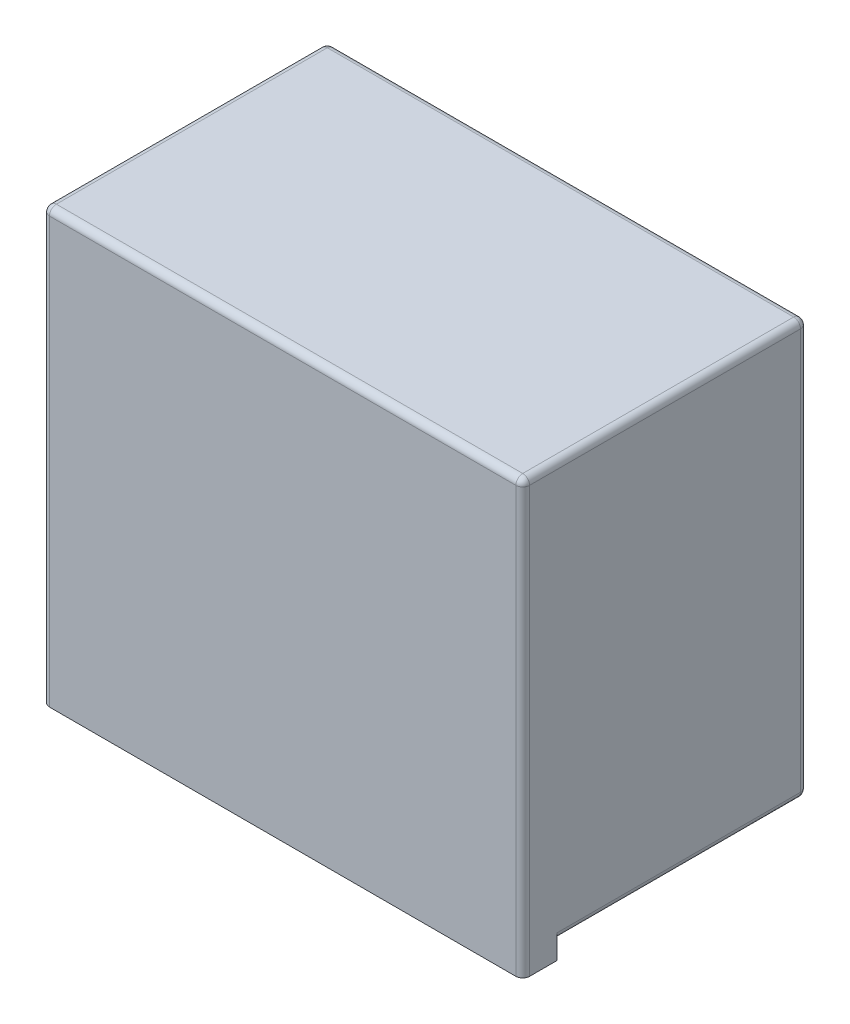
SolidWorks part; units mm, degrees
material "Duranickel(R) 301"
ref_plane "Alzado" through (0, 0, 0) normal (0, 0, 1) x (1, 0, 0)
ref_plane "Planta" through (0, 0, 0) normal (0, 1, 0) x (1, 0, 0)
ref_plane "Vista lateral" through (0, 0, 0) normal (1, 0, 0) x (0, 0, -1)
sketch "Croquis1" plane through (0, 0, 0) normal (0, 0, 1) x (1, 0, 0)
  line L1 (0, 0) -> (14, 0)
  line L2 (0, 0) -> (0, 12.6)
  line L3 (0, 12.6) -> (14, 12.6)
  line L4 (14, 0) -> (14, 12.6)
  dimension "D1" = 14
  dimension "D2" = 12.6
extrude "Extruir1" add sketch "Croquis1" along normal blind 8.3
sketch "Croquis2" plane through (0, 0, 0) normal (0, 0, -1) x (-1, 0, 0)
  line L0 (-14.677, 10.9) -> (-1.1655, 10.9) construction
  line L1 (-14, 12.6) -> (0, 12.6) construction
  line L2 (-7, 0) -> (-7, -0.6221) construction
  line L3 (0, 0) -> (-14, 0) construction
  circle A0 centre (-7, 6.15) radius 4.75
  dimension "D1" = 9.5
  dimension "D2" = 1.7
extrude "Cortar-Extruir1" cut sketch "Croquis2" against normal blind 7.3
fillet "Redondeo1" radius 0.5 1 edges at (2.25, 6.15, 0)
sketch "Croquis3" plane through (0, 0, 0) normal (0, 0, -1) x (-1, 0, 0)
  line L0 (-7, 1.4) -> (-4.2619, 1.4) construction
  line L2 (-14, 0) -> (-14, 12.6) construction
  line L3 (-11.6, 0.5) -> (-2.4, 0.5)
  line L4 (-11.6, 0.5) -> (-11.6, -0.2894)
  line L5 (-11.6, -0.2894) -> (-2.4, -0.2894)
  line L6 (-2.4, 0.5) -> (-2.4, -0.2894)
  line L7 (-1, 0.5) -> (1.0352, 0.5)
  line L8 (-1, 0.5) -> (-1, -0.2894)
  line L9 (-1, -0.2894) -> (1.0352, -0.2894)
  line L10 (1.0352, 0.5) -> (1.0352, -0.2894)
  line L11 (-14.7281, 0.5) -> (-13, 0.5)
  line L12 (-14.7281, 0.5) -> (-14.7281, -0.6477)
  line L13 (-14.7281, -0.6477) -> (-13, -0.6477)
  line L14 (-13, 0.5) -> (-13, -0.6477)
  line L15 (0, 12.6) -> (0, 0) construction
  line L16 (0, 0) -> (-14, 0) construction
  circle A2 centre (-7, 6.15) radius 4.75 construction
  circle A3 centre (-7, 6.15) radius 4.75 construction
  dimension "D1" = 1.4
  dimension "D2" = 1
  dimension "D3" = 1
  dimension "D4" = 1.4
  dimension "D5" = 0.5
extrude "Cortar-Extruir2" cut sketch "Croquis3" against normal blind 7.3
fillet "Redondeo2" radius 0.5 2 edges at (1.7, 0, 0) (12.3, 0, 0)
sketch "Croquis4" plane through (0, 0, 0) normal (0, 0, -1) x (-1, 0, 0)
  line L0 (-7, 2.3) -> (-2.1635, 2.3) construction
  line L1 (-10.5242, 4.6) -> (-9.35, 4.6)
  line L4 (-9.35, 4.6) -> (-9.35, 3.1004)
  line L5 (-7, 10) -> (-7, 10.5095) construction
  line L6 (-4.65, 4.6) -> (-4.65, 3.1004)
  line L9 (-3.4758, 4.6) -> (-4.65, 4.6)
  line L12 (-7.9, 9.8933) -> (-7.9, 9.3)
  line L13 (-7.9, 9.3) -> (-6.1, 9.3)
  line L14 (-6.1, 9.8933) -> (-6.1, 9.3)
  arc A0 (-3.4758, 4.6) -> (-6.1, 9.8933) centre (-7, 6.15) ccw
  arc A1 (-9.35, 3.1004) -> (-4.65, 3.1004) centre (-7, 6.15) ccw
  arc A2 (-7.9, 9.8933) -> (-10.5242, 4.6) centre (-7, 6.15) ccw
  dimension "D1" = 7.7
  dimension "D2" = 2.35
  dimension "D3" = 2.3
  dimension "D4" = 4.7
  dimension "D6" = 0.9
extrude "Extruir2" add sketch "Croquis4" against normal up to surface (7.3 mm away) separate body up to face at (2.25, 6.15, 7.3)
sketch "Croquis5" plane through (0, 0, 0) normal (0, 0, -1) x (-1, 0, 0)
  line L0 (-6.1, 9.3) -> (-7.9, 9.3) construction
  line L1 (-7.75, 8.5) -> (-6.25, 8.5)
  line L2 (-7.75, 8.5) -> (-7.75, 6.3)
  line L3 (-7.75, 6.3) -> (-6.25, 6.3)
  line L4 (-6.25, 8.5) -> (-6.25, 6.3)
  line L6 (-6.25, 8.5) -> (-6.25, 6.3)
  circle A0 centre (-8.2283, 3.7538) radius 0.3
  circle A1 centre (-9.7381, 5.7754) radius 0.3
  circle A2 centre (-9.3287, 8.0017) radius 0.3
  circle A3 centre (-4.6713, 8.0017) radius 0.3
  circle A4 centre (-4.2619, 5.7754) radius 0.3
  circle A5 centre (-5.7717, 3.7538) radius 0.3
  dimension "D5" = 0.6
  dimension "D6" = 0.6
  dimension "D7" = 0.6
  dimension "D1" = 0.8
  dimension "D2" = 2.2
  dimension "D3" = 1.5
extrude "Cortar-Extruir3" cut sketch "Croquis5" against normal blind 7.3 contours L4 L1 L2 L3 | A3 | A4 | A2 | A1 | A0 | A5
chamfer "Chaflán1" distance 0.4 angle 45 6 edges at (3.9619, 5.7754, 0) (4.3713, 8.0017, 0) (9.0287, 8.0017, 0) (9.4381, 5.7754, 0) (5.4717, 3.7538, 0) (7.9283, 3.7538, 0)
fillet "Redondeo3" radius 0.2 13 edges at (0.5, 0.5, 0) (7, 0.5, 0) (14, 0.5, 3.65) (0, 0.5, 3.65) (13.5, 0.5, 0) (0, 6.3, 8.3) (0, 12.6, 4.15) (7, 12.6, 8.3) (14, 6.3, 8.3) (14, 12.6, 4.15) (0, 6.55, 0) (14, 6.55, 0) (7, 12.6, 0)
